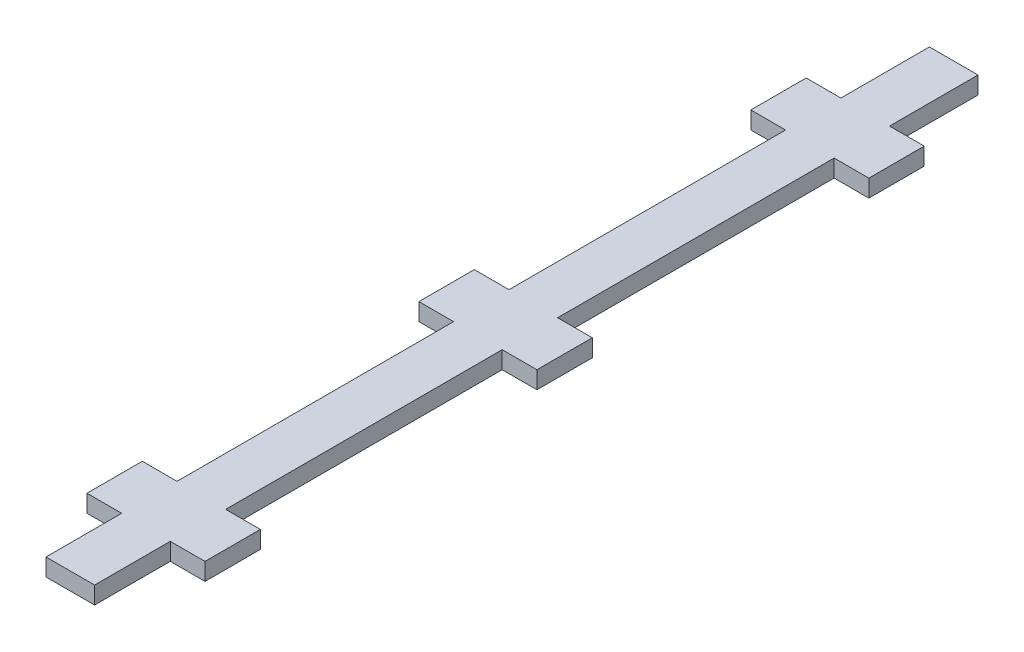
SolidWorks part; units mm, degrees
ref_plane "Front Plane" through (0, 0, 0) normal (0, 0, 1) x (1, 0, 0)
ref_plane "Top Plane" through (0, 0, 0) normal (0, 1, 0) x (1, 0, 0)
ref_plane "Right Plane" through (0, 0, 0) normal (1, 0, 0) x (0, 0, -1)
sketch "Sketch1" plane through (0, 0, 0) normal (0, 1, 0) x (1, 0, 0)
  line L0 (4.445, 0) -> (-4.445, 0)
  line L1 (-4.445, 0) -> (-4.445, 13.843)
  line L2 (-4.445, 13.843) -> (-10.795, 13.843)
  line L3 (-10.795, 13.843) -> (-10.795, 23.9749)
  line L4 (0, 0) -> (0, 182.3648) construction
  line L5 (-4.445, 0) -> (-4.445, 182.3648) construction
  line L6 (-10.795, 23.9749) -> (-4.445, 23.9749)
  line L7 (-4.445, 23.9749) -> (-4.445, 74.5649)
  line L8 (-4.445, 74.5649) -> (-10.795, 74.5649)
  line L9 (-10.795, 74.5649) -> (-10.795, 84.6968)
  line L10 (-10.795, 84.6968) -> (-4.445, 84.6968)
  line L11 (-4.445, 84.6968) -> (-4.445, 135.2868)
  line L12 (-4.445, 135.2868) -> (-10.795, 135.2868)
  line L13 (-10.795, 135.2868) -> (-10.795, 145.4186)
  line L14 (-10.795, 145.4186) -> (-4.445, 145.4186)
  line L15 (-4.445, 145.4186) -> (-4.445, 161.6053)
  line L16 (-4.445, 161.6053) -> (4.445, 161.6053)
  line L17 (4.445, 0) -> (4.445, 13.843)
  line L18 (4.445, 13.843) -> (10.795, 13.843)
  line L19 (10.795, 13.843) -> (10.795, 23.9749)
  line L20 (10.795, 23.9749) -> (4.445, 23.9749)
  line L21 (4.445, 23.9749) -> (4.445, 74.5649)
  line L22 (4.445, 74.5649) -> (10.795, 74.5649)
  line L23 (10.795, 74.5649) -> (10.795, 84.6968)
  line L24 (10.795, 84.6968) -> (4.445, 84.6968)
  line L25 (4.445, 84.6968) -> (4.445, 135.2868)
  line L26 (4.445, 135.2868) -> (10.795, 135.2868)
  line L27 (10.795, 135.2868) -> (10.795, 145.4186)
  line L28 (10.795, 145.4186) -> (4.445, 145.4186)
  line L29 (4.445, 145.4186) -> (4.445, 161.6053)
  point P33 (0, 161.6053)
  dimension "D1" = 4.445
  dimension "D2" = 13.843
  dimension "D3" = 50.59
  dimension "D4" = 10.1319
  dimension "D5" = 6.35
  dimension "D6" = 16.1866
extrude "Boss-Extrude1" add sketch "Sketch1" along normal blind 3.175
